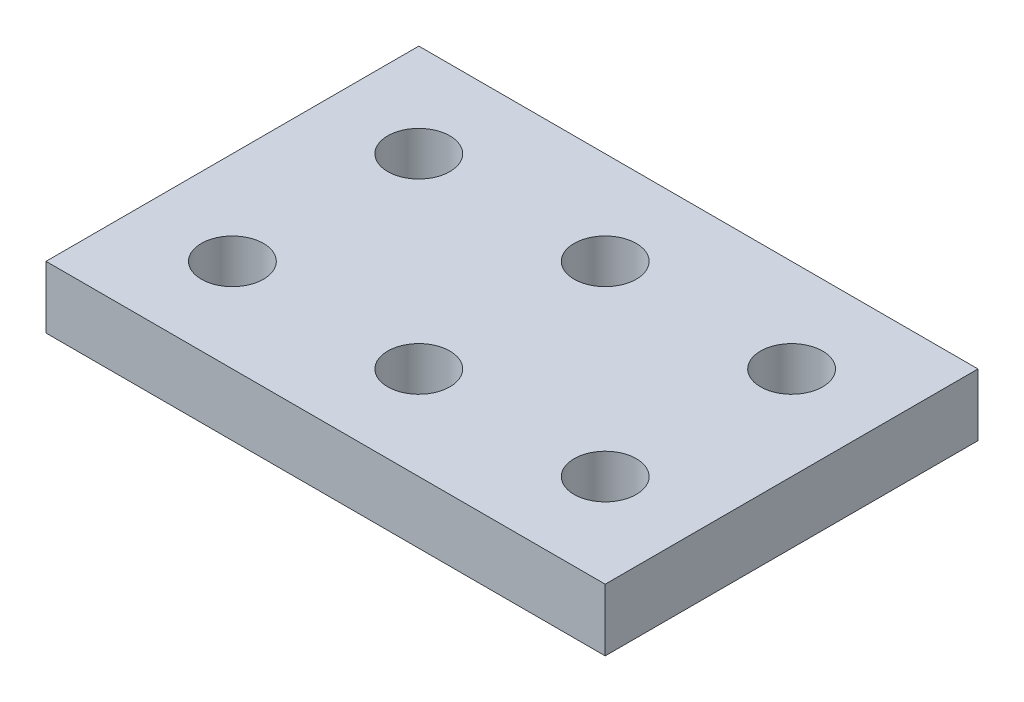
SolidWorks part; units mm, degrees
ref_plane "Front Plane" through (0, 0, 0) normal (0, 0, 1) x (1, 0, 0)
ref_plane "Top Plane" through (0, 0, 0) normal (0, 1, 0) x (1, 0, 0)
ref_plane "Right Plane" through (0, 0, 0) normal (1, 0, 0) x (0, 0, -1)
sketch "Sketch1" plane through (0, 0, 0) normal (0, 1, 0) x (1, 0, 0)
  line L1 (0, 0) -> (90, 0)
  line L2 (0, 0) -> (0, 60)
  line L3 (0, 60) -> (90, 60)
  line L4 (90, 0) -> (90, 60)
  dimension "D1" = 90
  dimension "D2" = 60
extrude "Boss-Extrude1" add sketch "Sketch1" along normal blind 10
sketch "Sketch2" plane through (0, 10, 0) normal (0, 1, 0) x (1, 0, 0)
  line L0 (0, 0) -> (90, 0) construction
  line L1 (0, 60) -> (0, 0) construction
  circle A0 centre (15, 15) radius 5
  dimension "D1" = 15
  dimension "D2" = 15
  dimension "D3" = 10
extrude "Cut-Extrude1" cut sketch "Sketch2" against normal through all
pattern_linear "LPattern1" count 4 spacing 30 along (1, 0, 0) count 4 spacing 30 along (0, 0, -1) of "Cut-Extrude1"
